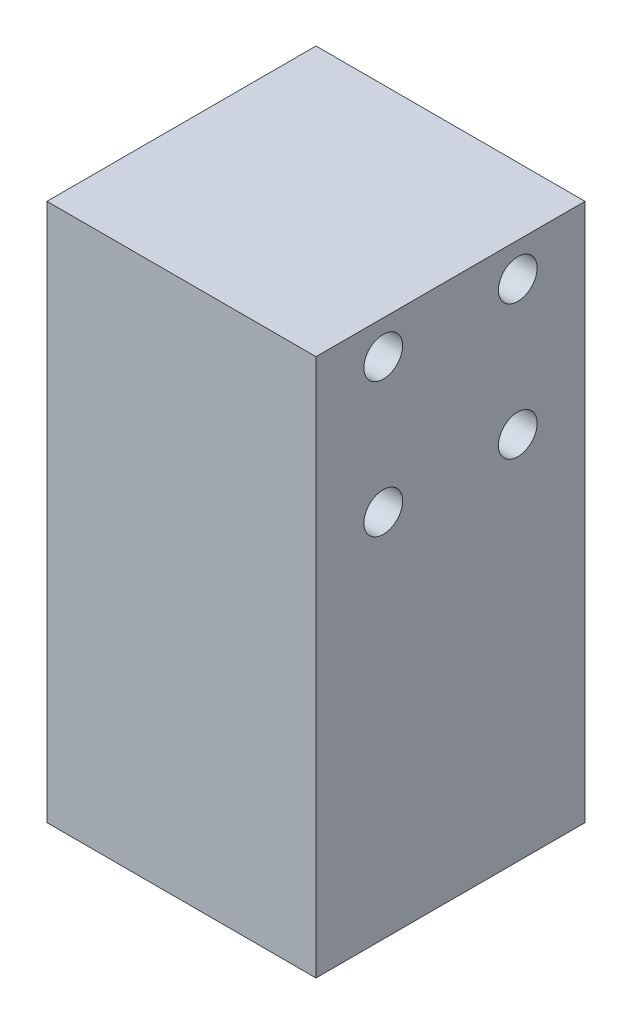
SolidWorks part; units mm, degrees
ref_plane "Front Plane" through (0, 0, 0) normal (0, 0, 1) x (1, 0, 0)
ref_plane "Top Plane" through (0, 0, 0) normal (0, 1, 0) x (1, 0, 0)
ref_plane "Right Plane" through (0, 0, 0) normal (1, 0, 0) x (0, 0, -1)
sketch "Sketch1" plane through (0, 0, 0) normal (0, 1, 0) x (1, 0, 0)
  line L1 (-12.7, -12.7) -> (12.7, -12.7)
  line L2 (-12.7, -12.7) -> (-12.7, 12.7)
  line L3 (-12.7, 12.7) -> (12.7, 12.7)
  line L4 (12.7, -12.7) -> (12.7, 12.7)
  line L5 (-12.7, -12.7) -> (12.7, 12.7) construction
  line L6 (-12.7, 12.7) -> (12.7, -12.7) construction
  point P0 (0, 0)
  dimension "D1" = 25.4
  dimension "D2" = 25.4
extrude "Boss-Extrude1" add sketch "Sketch1" along normal blind 50.8
sketch "Sketch2" plane through (12.7, 0, 0) normal (1, 0, 0) x (0, 0, -1)
  line L0 (-6.35, 47.625) -> (6.35, 47.625) construction
  line L1 (-6.35, 47.625) -> (-6.35, 34.925) construction
  line L2 (-6.35, 34.925) -> (6.35, 34.925) construction
  line L3 (6.35, 47.625) -> (6.35, 34.925) construction
  line L4 (-12.7, 50.8) -> (12.7, 50.8) construction
  line L5 (-12.7, 50.8) -> (-12.7, 0) construction
  circle A0 centre (-6.35, 47.625) radius 1.8288
  circle A1 centre (6.35, 47.625) radius 1.8288
  circle A2 centre (6.35, 34.925) radius 1.8288
  circle A3 centre (-6.35, 34.925) radius 1.8288
  dimension "D1" = 3.6576
  dimension "D2" = 12.7
  dimension "D3" = 3.175
  dimension "D4" = 6.35
extrude "Cut-Extrude1" cut sketch "Sketch2" against normal blind 12.7
sketch "Sketch3" plane through (0, 0, 0) normal (0, -1, 0) x (1, 0, 0)
  line L0 (-6.35, 6.35) -> (6.35, 6.35) construction
  line L1 (-6.35, 6.35) -> (-6.35, -6.35) construction
  line L2 (-6.35, -6.35) -> (6.35, -6.35) construction
  line L3 (6.35, 6.35) -> (6.35, -6.35) construction
  line L4 (-6.35, 6.35) -> (6.35, -6.35) construction
  line L5 (-6.35, -6.35) -> (6.35, 6.35) construction
  circle A0 centre (-6.35, 6.35) radius 1.8288
  circle A1 centre (6.35, 6.35) radius 1.8288
  circle A2 centre (6.35, -6.35) radius 1.8288
  circle A3 centre (-6.35, -6.35) radius 1.8288
  dimension "D1" = 3.6576
  dimension "D2" = 12.7
extrude "Cut-Extrude2" cut sketch "Sketch3" against normal blind 12.7
